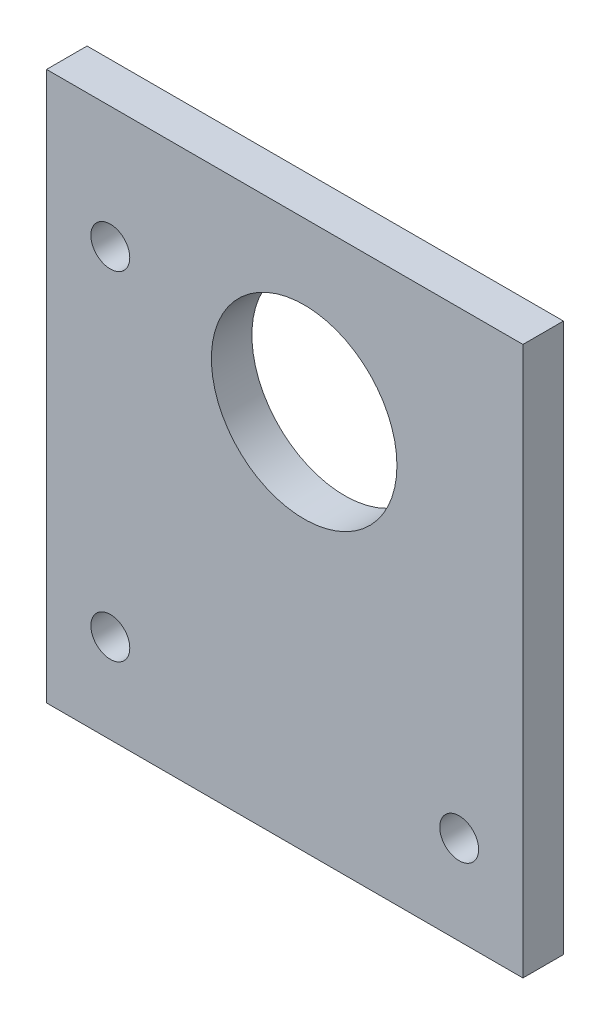
SolidWorks part; units mm, degrees
material "ASTM A36 Steel"
ref_plane "Front Plane" through (0, 0, 0) normal (0, 0, 1) x (1, 0, 0)
ref_plane "Top Plane" through (0, 0, 0) normal (0, 1, 0) x (1, 0, 0)
ref_plane "Right Plane" through (0, 0, 0) normal (1, 0, 0) x (0, 0, -1)
sketch "Sketch1" plane through (0, 0, 0) normal (0, 0, 1) x (1, 0, 0)
  line L1 (5.5978, 13.2827) -> (5.5978, 26.3124)
  line L2 (5.5978, 26.3124) -> (20.32, 26.3124)
  line L3 (21.59, 25.0424) -> (21.59, 0)
  line L4 (0, -21.59) -> (-39.1074, -21.59)
  line L6 (-40.3774, -20.32) -> (-40.3774, 25.0424)
  line L7 (-39.1074, 26.3124) -> (-34.2539, 26.3124)
  line L8 (-34.2539, 26.3124) -> (-14.5989, 2.3182)
  line L9 (-40.3774, 26.3124) -> (21.59, 26.3124)
  line L10 (21.59, 26.3124) -> (21.59, -21.59)
  line L11 (21.59, -21.59) -> (-40.3774, -21.59)
  line L12 (-40.3774, -21.59) -> (-40.3774, 26.3124)
  line L13 (21.59, -21.59) -> (34.29, -21.59)
  line L14 (34.29, -21.59) -> (34.29, 26.3124)
  line L15 (34.29, 26.3124) -> (21.59, 26.3124)
  line L16 (21.59, -21.59) -> (34.29, -21.59)
  line L17 (21.59, 26.3124) -> (21.59, -21.59)
  line L18 (-40.3774, -21.59) -> (-40.3774, -59.69)
  line L19 (-40.3774, -59.69) -> (34.29, -59.69)
  line L20 (34.29, -59.69) -> (34.29, -21.59)
  circle A0 centre (0, 0) radius 19.05 construction
  circle A1 centre (0, 0) radius 14.5415
  arc A2 (-12.3786, 2.839) -> (3.9343, 12.0752) centre (0, 0) cw
  arc A5 (21.59, 0) -> (0, -21.59) centre (0, 0) cw
  arc A6 (-12.3786, 2.839) -> (-14.5989, 2.3182) centre (-13.6165, 3.1229) cw
  arc A7 (3.9343, 12.0752) -> (5.5978, 13.2827) centre (4.3278, 13.2827) ccw
  arc A8 (20.32, 26.3124) -> (21.59, 25.0424) centre (20.32, 25.0424) cw
  arc A9 (-40.3774, 25.0424) -> (-39.1074, 26.3124) centre (-39.1074, 25.0424) cw
  arc A10 (-39.1074, -21.59) -> (-40.3774, -20.32) centre (-39.1074, -20.32) cw
  circle A11 centre (-30.3825, -45.72) radius 3.048
  circle A12 centre (24.2951, -45.72) radius 3.048
  circle A13 centre (-30.3825, 7.2624) radius 3.048
  point P22 (-12.7, 0)
  dimension "D1" = 38.1
  dimension "D2" = 29.083
  dimension "D3" = 21.59
  dimension "D4" = 12.7
  dimension "D5" = 1.27
  dimension "D6" = 1.27
  dimension "D7" = 1.27
  dimension "D12" = 6.096
  dimension "D13" = 6.096
  dimension "D16" = 6.096
  dimension "D8" = 12.7
  dimension "D9" = 38.1
  dimension "D10" = 9.9949
  dimension "D11" = 13.97
  dimension "D14" = 9.9949
  dimension "D15" = 13.97
  dimension "D17" = 9.9949
  dimension "D18" = 19.05
extrude "Boss-Extrude1" add sketch "Sketch1" along normal blind 6.35 contours A10 L4 A5 L3 A8 L2 L1 A7 A2 A6 L8 L7 A9 L6 A1 | L10 A5 L11 | L12 A9 L9 | L9 A8 L10 | L11 A10 L12 | A2 A7 L1 L9 L8 A6 | L14 L15 L10 L3 L13 | L19 L20 L13 L11 L4 L18
